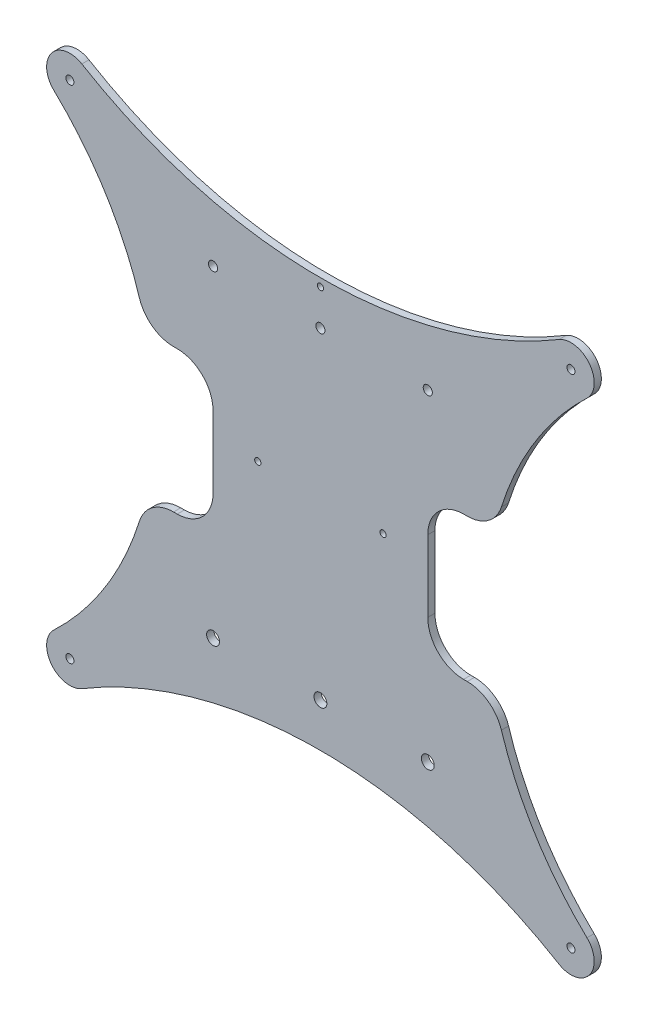
SolidWorks part; units mm, degrees
material "6061 合金"
ref_plane "前视基准面" through (0, 0, 0) normal (0, 0, 1) x (1, 0, 0)
ref_plane "上视基准面" through (0, 0, 0) normal (0, 1, 0) x (1, 0, 0)
ref_plane "右视基准面" through (0, 0, 0) normal (1, 0, 0) x (0, 0, -1)
sketch "草图1" plane through (0, 0, 0) normal (0, 0, 1) x (1, 0, 0)
  line L0 (0, 0) -> (15857.2726, 0) construction
  line L1 (0, 0) -> (0, 15857.2726) construction
  circle A0 centre (0, 90) radius 2.55
  circle A1 centre (0, -90) radius 3.6
  circle A2 centre (60, 90) radius 2.55
  circle A3 centre (60, -90) radius 3.6
  circle A4 centre (-60, 90) radius 2.55
  circle A5 centre (-60, -90) radius 3.6
  circle A6 centre (-140, 140) radius 2.25
  circle A7 centre (140, 140) radius 2.25
  circle A8 centre (-140, -140) radius 2.25
  circle A9 centre (140, -140) radius 2.25
  arc A10 (-133.3333, 151.1604) -> (-148.9484, 130.5699) centre (-140, 140) ccw
  arc A11 (148.9484, 130.5699) -> (133.3333, 151.1604) centre (140, 140) ccw
  arc A12 (133.3333, -151.1604) -> (148.9484, -130.5699) centre (140, -140) ccw
  arc A13 (-148.9484, -130.5699) -> (-133.3333, -151.1604) centre (-140, -140) ccw
  arc A14 (-148.9484, -130.5699) -> (-148.9484, 130.5699) centre (-272.8495, 0) ccw
  arc A15 (148.9484, -130.5699) -> (148.9484, 130.5699) centre (272.8495, 0) cw
  circle A16 centre (-35, 8) radius 1.75
  circle A17 centre (35, 8) radius 1.75
  arc A18 (-133.3333, 151.1604) -> (133.3333, 151.1604) centre (0, 374.3694) ccw
  arc A19 (-133.3333, -151.1604) -> (133.3333, -151.1604) centre (0, -374.3694) cw
  circle A20 centre (0, 110) radius 1.75
  circle A22 centre (-140, -140) radius 2.25 [skipped]
  circle A23 centre (140, -140) radius 2.25 [skipped]
  point P28 (0, 0)
  point P36 (0, 0)
  dimension "D1" = 90
  dimension "D2" = 90
  dimension "D3" = 5.1
  dimension "D4" = 7.2
  dimension "D7" = 4.5
  dimension "D11" = 26
  dimension "D15" = 520
  dimension "D14" = 180
  dimension "D20" = 3.5
  dimension "D12" = 60
  dimension "D16" = 8
  dimension "D17" = 3.5
  dimension "D8" = 140
  dimension "D9" = 140
  dimension "D13" = 60
  dimension "D18" = 35
  dimension "D19" = 35
  dimension "D21" = 20
  dimension "D5" = 2
  dimension "D6" = 2
  dimension "D10" = 4
extrude "凸台-拉伸1" add sketch "草图1" along normal blind 4
sketch "草图2" plane through (0, 0, 4) normal (0, 0, 1) x (1, 0, 0)
  line L0 (-120.7304, -40) -> (-60, -40)
  line L1 (-60, -40) -> (-60, 40)
  line L2 (-60, 40) -> (-120.7304, 40)
  line L3 (-120.7304, 40) -> (-120.7304, -40)
  line L4 (146.2152, 0) -> (-143.4606, 0) construction
  line L5 (0, -190.1442) -> (0, 187.0296) construction
  line L6 (60, -40) -> (60, 40)
  line L7 (120.7304, -40) -> (60, -40)
  line L8 (60, 40) -> (120.7304, 40)
  line L9 (120.7304, 40) -> (120.7304, -40)
  dimension "D1" = 80
  dimension "D2" = 60
extrude "切除-拉伸1" cut sketch "草图2" against normal blind 10
fillet "圆角1" radius 20 8 edges at (97.3503, 40, 2) (60, 40, 2) (60, -40, 2) (97.3503, -40, 2) (-60, -40, 2) (-60, 40, 2) (-97.3503, 40, 2) (-97.3503, -40, 2)
